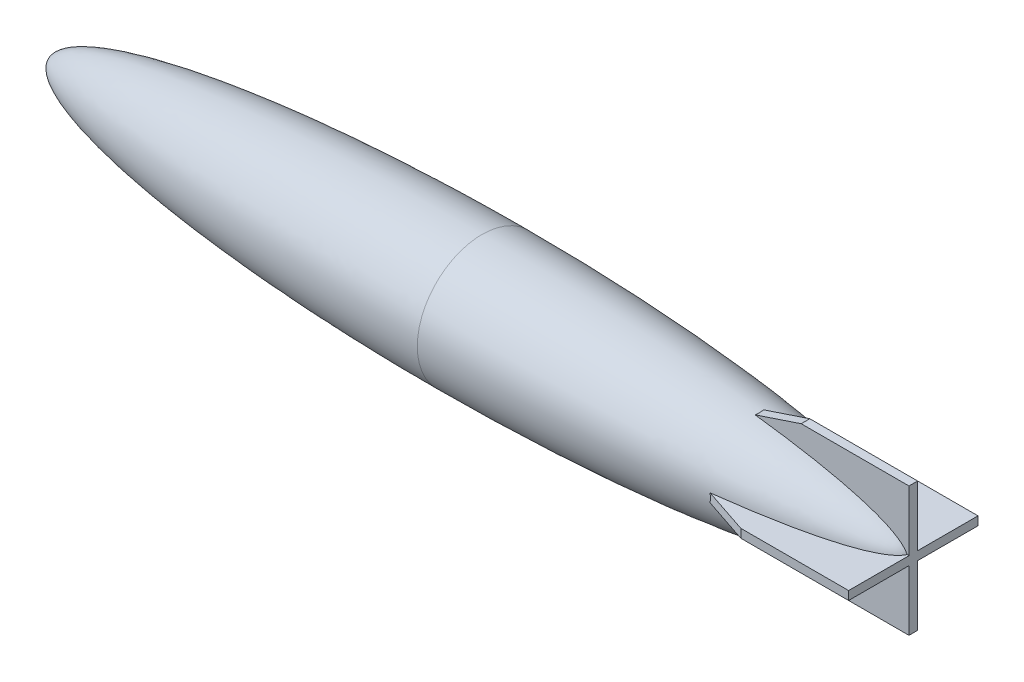
SolidWorks part; units mm, degrees
ref_plane "Front Plane" through (0, 0, 0) normal (0, 0, 1) x (1, 0, 0)
ref_plane "Top Plane" through (0, 0, 0) normal (0, 1, 0) x (1, 0, 0)
ref_plane "Right Plane" through (0, 0, 0) normal (1, 0, 0) x (0, 0, -1)
sketch "Sketch1" plane through (0, 0, 0) normal (0, 0, 1) x (1, 0, 0)
  line L0 (0, 0) -> (63.5, 0)
  line L1 (63.5, 0) -> (63.5, 9.525)
  spline S0 degree 4 poles (0, 0) (0, 0.0614) (0.0057, 0.1609) (0.0271, 0.3026) (0.0791, 0.4869) (0.1482, 0.6607) (0.2498, 0.8541) (0.3958, 1.0723) (0.6074, 1.326) (0.9183, 1.6278) (1.3859, 1.9965) (2.1175, 2.4626) (3.2833, 3.055) (5.1471, 3.7989) (8.0324, 4.6892) (11.8337, 5.5855) (16.3498, 6.4186) (21.2771, 7.1425) (26.2195, 7.7333) (31.1769, 8.2174) (36.1363, 8.6119) (40.49, 8.8884) (44.2093, 9.0812) (47.3336, 9.2141) (49.7916, 9.3043) (52.3351, 9.3789) (54.7281, 9.4381) (57.3776, 9.4822) (59.5973, 9.5116) (62.7414, 9.5272) (64.525, 9.5259) (67.0802, 9.5133) (68.338, 9.4964) (69.3402, 9.486) (69.6009, 9.4802) (69.8617, 9.4773) knots 0 0 0 0 0 0.003408 0.00555 0.00795 0.010644 0.013801 0.017688 0.022543 0.029003 0.037877 0.05078 0.070759 0.101702 0.149452 0.218741 0.288029 0.357317 0.426605 0.495893 0.565181 0.634469 0.669113 0.703757 0.738401 0.773045 0.807689 0.842333 0.876977 0.911621 0.95581 0.977905 0.988953 1 1 1 1 1 construction
  spline S1 degree 4 poles (0, 0) (0, 0.0614) (0.0057, 0.1609) (0.0271, 0.3026) (0.0791, 0.4869) (0.1482, 0.6607) (0.2498, 0.8541) (0.3958, 1.0723) (0.6074, 1.326) (0.9183, 1.6278) (1.3859, 1.9965) (2.1175, 2.4626) (3.2833, 3.055) (5.1471, 3.7989) (8.0324, 4.6892) (11.8337, 5.5855) (16.3498, 6.4186) (21.2771, 7.1425) (26.2195, 7.7333) (31.1769, 8.2174) (36.1363, 8.6119) (40.49, 8.8884) (44.2093, 9.0812) (47.3336, 9.2141) (49.7916, 9.3043) (52.3351, 9.3789) (54.7281, 9.4381) (57.3776, 9.4822) (59.5973, 9.5116) (61.8034, 9.5226) (62.9327, 9.525) (63.5, 9.525) knots 0 0 0 0 0 0.003408 0.00555 0.00795 0.010644 0.013801 0.017688 0.022543 0.029003 0.037877 0.05078 0.070759 0.101702 0.149452 0.218741 0.288029 0.357317 0.426605 0.495893 0.565181 0.634469 0.669113 0.703757 0.738401 0.773045 0.807689 0.842333 0.876977 0.911621 0.911621 0.911621 0.911621 0.911621
  dimension "D1" = 9.525
revolve "Revolve1" add sketch "Sketch1" angle 360 about L0
ref_plane "Plane1" through (63.5, 0, 0) normal (1, 0, 0) x (0, 0, -1)
mirror "Mirror1" about plane through (63.5, 0, 0) normal (1, 0, 0) of "Revolve1"
sketch "Sketch3" plane through (0, 0, 0) normal (0, 0, 1) x (1, 0, 0)
  line L0 (127, 9.525) -> (111.125, 9.525)
  line L1 (111.125, 9.525) -> (82.55, 0)
  line L2 (82.55, 0) -> (111.125, -9.525)
  line L3 (111.125, -9.525) -> (127, -9.525)
  line L4 (127, -9.525) -> (127, 9.525)
  point P6 (127, 0)
  dimension "D1" = 15.875
  dimension "D2" = 44.45
extrude "Boss-Extrude2" add sketch "Sketch3" along normal mid plane 1.27
pattern_circular "CirPattern1" count 2 every 90 about axis through (0, 0, 0) along (1, 0, 0) of "Boss-Extrude2"
